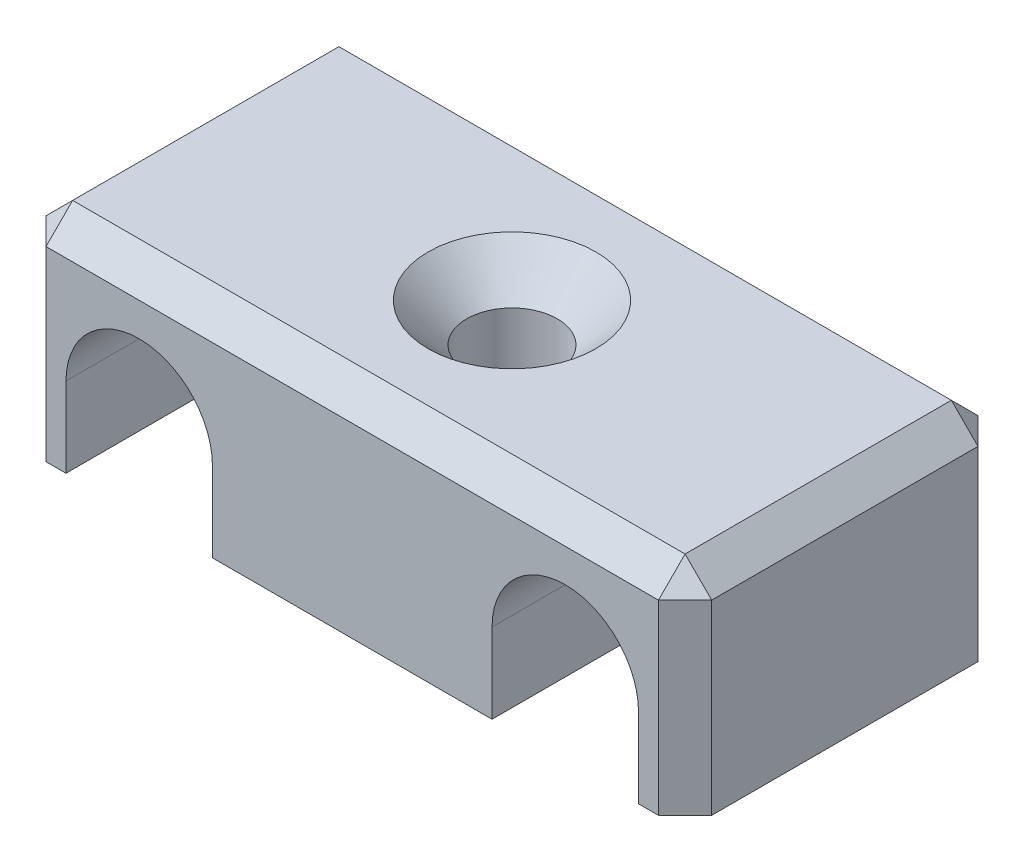
SolidWorks part; units mm, degrees
ref_plane "Plan de face" through (0, 0, 0) normal (0, 0, 1) x (1, 0, 0)
ref_plane "Plan de dessus" through (0, 0, 0) normal (0, 1, 0) x (1, 0, 0)
ref_plane "Plan de droite" through (0, 0, 0) normal (1, 0, 0) x (0, 0, -1)
sketch "Esquisse1" plane through (0, 0, 0) normal (0, 0, 1) x (1, 0, 0)
  line L1 (-12.5, -4) -> (12.5, -4)
  line L2 (-12.5, -4) -> (-12.5, 4)
  line L3 (-12.5, 4) -> (12.5, 4)
  line L4 (12.5, -4) -> (12.5, 4)
  line L5 (-12.5, -4) -> (12.5, 4) construction
  line L6 (-12.5, 4) -> (12.5, -4) construction
  point P1 (0, 0)
  dimension "D1" = 25
  dimension "D2" = 8
extrude "Boss.-Extru.1" add sketch "Esquisse1" along normal blind 12
hole_wizard "Fraisage pour vis à tête fraisée M31" positions "Esquisse2" profile "Esquisse3" countersink size "M3" standard "Ansi Metric" end condition through all
sketch "Esquisse2" plane through (0, 4, 0) normal (0, 1, 0) x (1, 0, 0)
  line L0 (12.5, -12) -> (12.5, 0) construction
  point P0 (0, -6)
  point P6 (12.5, -6)
sketch "Esquisse3" plane through (0, 4, 6) normal (1, 0, 0) x (0, 0, 1)
  line L0 (0, 0) -> (0, 8)
  line L1 (0, 8) -> (1.7, 8)
  line L2 (1.7, 8) -> (1.7, 1.45)
  line L3 (1.7, 1.45) -> (3.15, 0)
  line L5 (3.15, 0) -> (0, 0)
  line L6 (-1.7, 1.45) -> (-3.15, 0) construction
  line L11 (0, -6.35) -> (0, 107.95) construction
  dimension "Diamètre du perçage jusqu'au prochain" = 3.4
  dimension "Profondeur du perçage jusqu'au prochain" = 8
  dimension "Diamètre du fraisage entrant" = 6.3
  dimension "Angle du fraisage entrant" = 90
sketch "Esquisse4" plane through (0, 0, 12) normal (0, 0, 1) x (1, 0, 0)
  line L0 (12.5, -4) -> (12.5, 4) construction
  line L1 (-12.5, 4) -> (-12.5, -4) construction
  line L3 (-12.5, -4) -> (12.5, -4) construction
  line L4 (-5.25, -1) -> (-5.25, -4)
  line L5 (5.25, -1) -> (5.25, -4)
  line L6 (-10.75, -1) -> (-10.75, -4)
  line L7 (10.75, -1) -> (10.75, -4)
  line L8 (-10.75, -4) -> (-5.25, -4)
  line L9 (5.25, -4) -> (10.75, -4)
  arc A0 (-5.25, -1) -> (-10.75, -1) centre (-8, -1) ccw
  arc A1 (10.75, -1) -> (5.25, -1) centre (8, -1) ccw
  dimension "D1" = 5.5
  dimension "D2" = 4.5
  dimension "D3" = 4.5
  dimension "D4" = 3
  dimension "D5" = 3
extrude "Enlèv. mat.-Extru.1" cut sketch "Esquisse4" against normal through all
chamfer "Chanfrein1" distance 1 angle 45 8 edges at (12.5, 0, 0) (12.5, 0, 12) (-12.5, 0, 0) (-12.5, 0, 12) (-12.5, 4, 6) (0, 4, 0) (12.5, 4, 6) (0, 4, 12)
